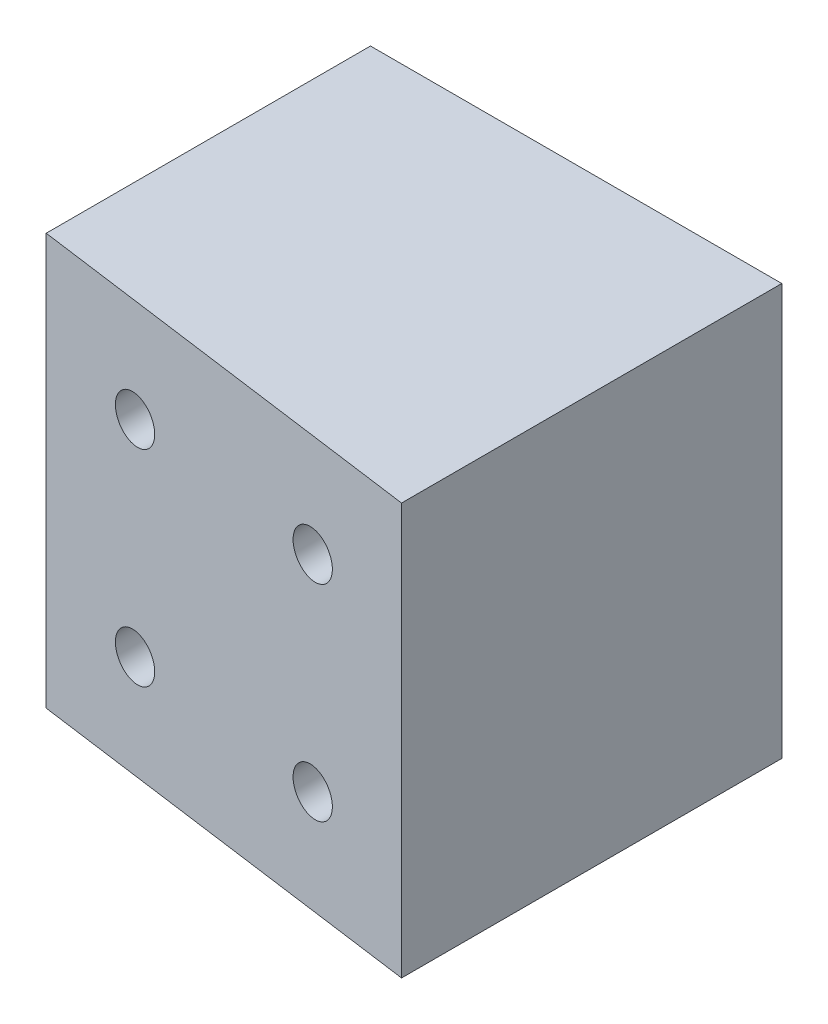
SolidWorks part; units mm, degrees
ref_plane "Front Plane" through (0, 0, 0) normal (0, 0, 1) x (1, 0, 0)
ref_plane "Top Plane" through (0, 0, 0) normal (0, 1, 0) x (1, 0, 0)
ref_plane "Right Plane" through (0, 0, 0) normal (1, 0, 0) x (0, 0, -1)
sketch "Sketch1" plane through (0, 0, 0) normal (0, 1, 0) x (1, 0, 0)
  line L1 (-94.6194, -34.0812) -> (138.1834, -65.7727) construction
  line L2 (0, 0) -> (-50.8, 0)
  line L3 (-50.8, -40.0463) -> (0, -46.9617)
  line L4 (0, 0) -> (0, -46.9617)
  line L5 (0, 0) -> (-50.8, 0) construction
  line L6 (-50.8, 0) -> (-50.8, -40.0463)
  dimension "D1" = 50.8
extrude "Boss-Extrude1" add sketch "Sketch1" along normal blind 50.8
sketch "Sketch3" plane through (0, 0, 0) normal (0, 0, -1) x (-1, 0, 0)
  line L0 (0, 50.8) -> (50.8, 0) construction
  line L3 (0, 0) -> (50.8, 50.8) construction
  line L4 (12.7, 38.1) -> (38.1, 38.1)
  line L5 (12.7, 38.1) -> (12.7, 12.7)
  line L6 (12.7, 12.7) -> (38.1, 12.7)
  line L7 (38.1, 38.1) -> (38.1, 12.7)
  dimension "D1" = 25.4
hole_wizard "CSK for #10 Flat Head Machine Screw (100)2" positions "Sketch6" profile "Sketch7" countersink size "#10" standard "ANSI Inch" end condition through all
sketch "Sketch6" plane through (295.342, -214.7951, 50.8) normal (0, 0, -1) x (-1, 0, 0)
  point P0 (333.442, 227.4951)
  point P2 (333.442, 252.8951)
  point P4 (333.442, 329.0951)
  point P6 (333.442, 354.4951)
sketch "Sketch7" plane through (-38.1, 12.7, 50.8) normal (1, 0, 0) x (0, -1, 0)
  line L0 (0, 0) -> (0, 50.8)
  line L1 (0, 50.8) -> (2.8067, 50.8)
  line L2 (2.8067, 50.8) -> (2.8067, 6.0833)
  line L3 (2.8067, 6.0833) -> (8.89, 0)
  line L4 (8.89, 0) -> (0, 0)
  line L5 (-2.8067, 6.0833) -> (-8.89, 0) construction
  line L6 (0, -6.35) -> (0, 107.95) construction
  dimension "Thru Hole Dia." = 5.6134
  dimension "Thru Hole Depth" = 50.8
  dimension "Near C'Sink Dia." = 17.78
  dimension "Near C'Sink Angle" = 90
hole_wizard "CSK for #10 Flat Head Machine Screw (100)3" positions "Sketch8" profile "Sketch9" countersink size "#10" standard "ANSI Inch" end condition through all
sketch "Sketch8" plane through (295.342, -316.3951, 53.34) normal (0, 0, -1) x (-1, 0, 0)
  point P0 (308.042, 252.8951)
  point P2 (308.042, 227.4951)
  point P4 (308.042, 329.0951)
  point P6 (308.042, 354.4951)
sketch "Sketch9" plane through (-12.7, -63.5, 53.34) normal (1, 0, 0) x (0, -1, 0)
  line L0 (0, 0) -> (0, 53.34)
  line L1 (0, 53.34) -> (2.8067, 53.34)
  line L2 (2.8067, 53.34) -> (2.8067, 6.0833)
  line L3 (2.8067, 6.0833) -> (8.89, 0)
  line L4 (8.89, 0) -> (0, 0)
  line L5 (-2.8067, 6.0833) -> (-8.89, 0) construction
  line L6 (0, -6.35) -> (0, 107.95) construction
  dimension "Thru Hole Dia." = 5.6134
  dimension "Thru Hole Depth" = 53.34
  dimension "Near C'Sink Dia." = 17.78
  dimension "Near C'Sink Angle" = 90
